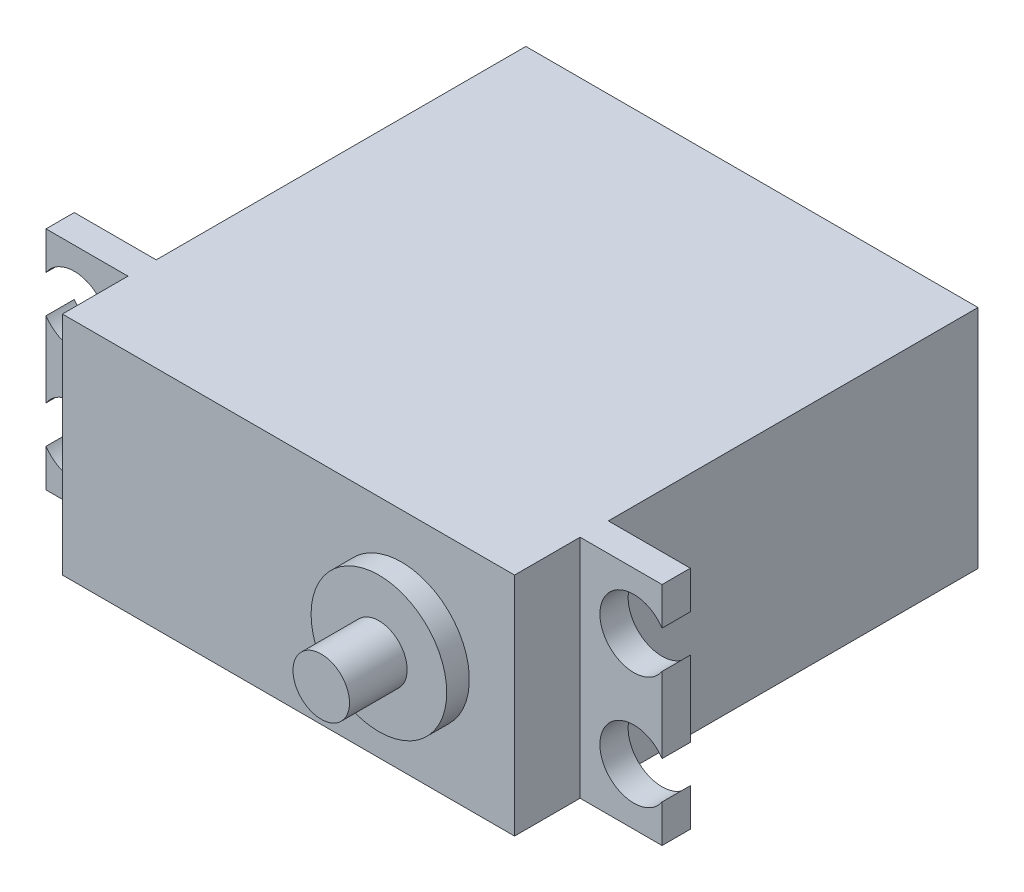
SolidWorks part; units mm, degrees
ref_plane "前视基准面" through (0, 0, 0) normal (0, 0, 1) x (1, 0, 0)
ref_plane "上视基准面" through (0, 0, 0) normal (0, 1, 0) x (1, 0, 0)
ref_plane "右视基准面" through (0, 0, 0) normal (1, 0, 0) x (0, 0, -1)
sketch "草图1" plane through (0, 0, 0) normal (0, 1, 0) x (1, 0, 0)
  line L1 (0, 0) -> (40, 0)
  line L2 (0, 0) -> (0, 41)
  line L3 (0, 41) -> (40, 41)
  line L4 (40, 0) -> (40, 41)
  dimension "D1" = 40
  dimension "D2" = 41
extrude "凸台-拉伸1" add sketch "草图1" along normal blind 20
sketch "草图2" plane through (0, 0, 0) normal (0, 0, 1) x (1, 0, 0)
  line L0 (40, 20) -> (40, 0) construction
  circle A0 centre (30, 10) radius 6
  dimension "D1" = 12
  dimension "D2" = 10
extrude "凸台-拉伸2" add sketch "草图2" along normal blind 2
sketch "草图3" plane through (0, 0, 2) normal (0, 0, 1) x (1, 0, 0)
  circle A0 centre (30, 10) radius 2.5
  dimension "D1" = 5
extrude "凸台-拉伸3" add sketch "草图3" along normal blind 5.1
sketch "草图4" plane through (0, 0, 0) normal (-1, 0, 0) x (0, 0, 1)
  line L0 (-41, 20) -> (0, 20) construction
  line L1 (-8.3, 20) -> (-5.8, 20)
  line L2 (-8.3, 20) -> (-8.3, 0)
  line L3 (-8.3, 0) -> (-5.8, 0)
  line L4 (-5.8, 20) -> (-5.8, 0)
  line L5 (-41, 0) -> (0, 0) construction
  line L6 (-41, 20) -> (-41, 0) construction
  dimension "D1" = 2.5
  dimension "D2" = 32.7
extrude "凸台-拉伸4" add sketch "草图4" along normal blind 7.25
sketch "草图5" plane through (0, 0, -5.8) normal (0, 0, 1) x (1, 0, 0)
  line L0 (-4.75, 20) -> (-4.75, 0) construction
  line L1 (-7.25, 20) -> (0, 20) construction
  line L2 (-7.25, 0) -> (0, 0) construction
  line L3 (-7.25, 10) -> (0, 10) construction
  line L4 (-7.25, 0) -> (-7.25, 20) construction
  line L5 (0, 0) -> (0, 20) construction
  line L6 (-7.25, 5) -> (0, 5) construction
  line L7 (-7.25, 15) -> (0, 15) construction
  circle A0 centre (-4.75, 15) radius 3
  circle A1 centre (-4.75, 5) radius 3
  dimension "D4" = 6
  dimension "D5" = 6
  dimension "D3" = 2.5
  dimension "D1" = 5
  dimension "D2" = 5
extrude "切除-拉伸2" cut sketch "草图5" against normal up to next (2.5 mm away)
ref_plane "基准面1" through (20, 0, 0) normal (-1, 0, 0) x (0, 0, 1)
mirror "镜向1" about plane through (20, 0, 0) normal (-1, 0, 0) of "切除-拉伸2", "凸台-拉伸4"
